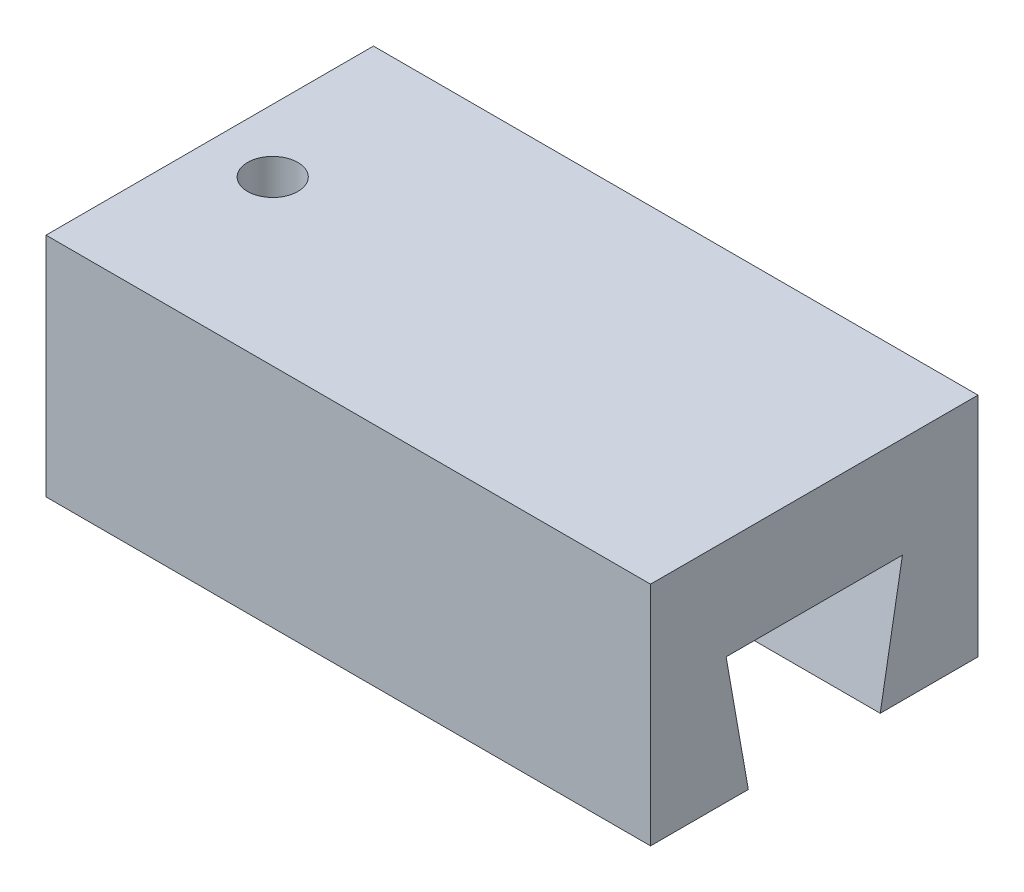
SolidWorks part; units mm, degrees
ref_plane "Front Plane" through (0, 0, 0) normal (0, 0, 1) x (1, 0, 0)
ref_plane "Top Plane" through (0, 0, 0) normal (0, 1, 0) x (1, 0, 0)
ref_plane "Right Plane" through (0, 0, 0) normal (1, 0, 0) x (0, 0, -1)
sketch "Sketch1" plane through (0, 0, 0) normal (0, 1, 0) x (1, 0, 0)
  line L1 (0, 0) -> (48, 0)
  line L2 (0, 0) -> (0, 26)
  line L3 (0, 26) -> (48, 26)
  line L4 (48, 0) -> (48, 26)
  dimension "D1" = 48
  dimension "D2" = 26
extrude "Boss-Extrude1" add sketch "Sketch1" along normal blind 18
sketch "Sketch2" plane through (48, 0, 0) normal (1, 0, 0) x (0, 0, -1)
  line L0 (0, 9) -> (26, 9) construction
  line L1 (0, 18) -> (0, 0) construction
  line L2 (26, 18) -> (26, 0) construction
  line L3 (13, 10) -> (13, 0)
  line L4 (6, 10) -> (20, 10)
  line L5 (20, 10) -> (18.2367, 0)
  line L6 (0, 0) -> (26, 0) construction
  line L7 (7.7633, 0) -> (18.2367, 0)
  line L8 (6, 10) -> (7.7633, 0)
  point P6 (17.6482, 0)
  line M5 (0, 0) -> (26, 0)
  dimension "D1" = 80
  dimension "D2" = 10
  dimension "D3" = 7
extrude "Cut-Extrude1" cut sketch "Sketch2" against normal through all both and the other way through all contours L0 L8 L3 M5 | L0 L3 L5 M5 | L3 L0 L5 L4 | L8 L0 L3 L4
sketch "Sketch3" plane through (0, 18, 0) normal (0, 1, 0) x (1, 0, 0)
  line L0 (0, 13) -> (48, 13) construction
  line L1 (0, 26) -> (0, 0) construction
  line L2 (48, 0) -> (48, 26) construction
  circle A0 centre (5, 13) radius 2
  dimension "D1" = 4
  dimension "D2" = 5
extrude "Cut-Extrude2" cut sketch "Sketch3" against normal through all both and the other way through all
